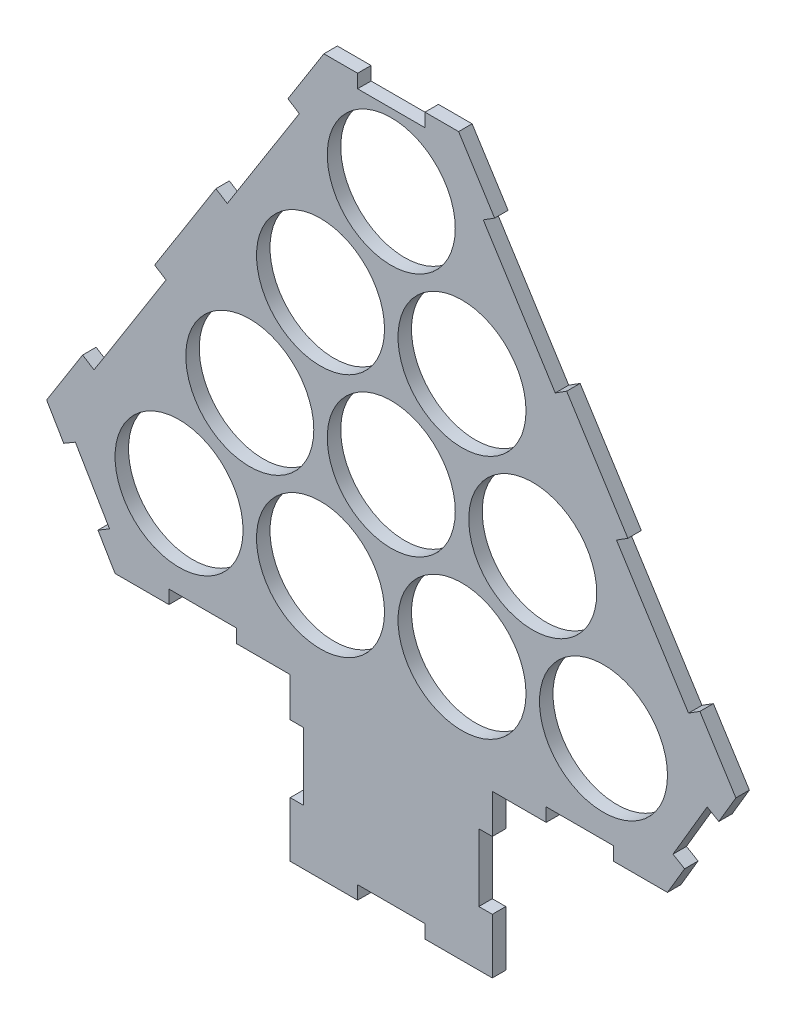
SolidWorks part; units mm, degrees
ref_plane "Plan de face" through (0, 0, 0) normal (0, 0, 1) x (1, 0, 0)
ref_plane "Plan de dessus" through (0, 0, 0) normal (0, 1, 0) x (1, 0, 0)
ref_plane "Plan de droite" through (0, 0, 0) normal (1, 0, 0) x (0, 0, -1)
sketch "Esquisse1" plane through (0, 0, 0) normal (0, 0, 1) x (1, 0, 0)
  line L0 (0, 0) -> (-371.1464, 0) construction
  line L1 (0, 0) -> (478.5179, 0) construction
  line L2 (0, 0) -> (0, 90.9327) construction
  line L3 (0, 90.9327) -> (-157.5, 90.9327) construction
  line L4 (0, 90.9327) -> (157.5, 90.9327) construction
  line L5 (0, 90.9327) -> (0, 181.8653) construction
  line L6 (0, 181.8653) -> (-52.5, 181.8653) construction
  line L7 (0, 181.8653) -> (52.5, 181.8653) construction
  line L8 (0, 181.8653) -> (0, 363.4062) construction
  line L12 (-255.7759, 10.9597) -> (-205, -75.1903)
  line L13 (205, -75.1903) -> (255.7759, 10.9597)
  line L14 (-50, 336.3537) -> (50, 336.3537)
  line L15 (-205, -75.1903) -> (205, -75.1903)
  line L16 (255.7759, 10.9597) -> (50, 336.3537)
  line L17 (-50, 336.3537) -> (-255.7759, 10.9597)
  line L18 (-50, 336.3537) -> (-50, -75.1903) construction
  line L19 (50, 336.3537) -> (50, -75.1903) construction
  circle A0 centre (-157.5, 0) radius 47.5
  circle A1 centre (-52.5, 0) radius 47.5
  circle A2 centre (52.5, 0) radius 47.5
  circle A3 centre (157.5, 0) radius 47.5
  circle A4 centre (-105, 90.9327) radius 47.5
  circle A5 centre (0, 90.9327) radius 47.5
  circle A6 centre (105, 90.9327) radius 47.5
  circle A7 centre (-52.5, 181.8653) radius 47.5
  circle A8 centre (52.5, 181.8653) radius 47.5
  circle A9 centre (0, 272.798) radius 47.5
  dimension "D1" = 95
  dimension "D2" = 95
  dimension "D3" = 95
  dimension "D4" = 95
  dimension "D5" = 105
  dimension "D6" = 52.5
  dimension "D7" = 52.5
  dimension "D8" = 105
  dimension "D9" = 95
  dimension "D10" = 95
  dimension "D11" = 95
  dimension "D12" = 105
  dimension "D13" = 105
  dimension "D14" = 105
  dimension "D15" = 95
  dimension "D16" = 95
  dimension "D17" = 105
  dimension "D18" = 52.5
  dimension "D19" = 52.5
  dimension "D20" = 95
  dimension "D21" = 105
  dimension "D27" = 205
  dimension "D22" = 385
  dimension "D23" = 385
  dimension "D24" = 410
  dimension "D25" = 32.309
  dimension "D26" = 32.309
  dimension "D28" = 100
  dimension "D30" = 100
  dimension "D31" = 100
extrude "Boss.-Extru.1" add sketch "Esquisse1" along normal blind 10
sketch "Esquisse9" plane through (0, 0, 10) normal (0, 0, 1) x (1, 0, 0)
  line L0 (-205, -75.1903) -> (205, -75.1903) construction
  line L1 (-75, -75.1903) -> (75, -75.1903)
  line L2 (-75, -75.1903) -> (-75, -195.1903)
  line L3 (-75, -195.1903) -> (75, -195.1903)
  line L4 (75, -75.1903) -> (75, -195.1903)
  dimension "D1" = 150
  dimension "D2" = 120
  dimension "D3" = 75
extrude "Boss.-Extru.2" add sketch "Esquisse9" against normal blind 10
sketch "Esquisse10" plane through (0, 0, 10) normal (0, 0, 1) x (1, 0, 0)
  line L0 (-75, -75.1903) -> (-75, -195.1903) construction
  line L1 (-75, -104.2447) -> (-65, -104.2447)
  line L2 (-75, -104.2447) -> (-75, -154.2447)
  line L3 (-75, -154.2447) -> (-65, -154.2447)
  line L4 (-65, -104.2447) -> (-65, -154.2447)
  line L5 (-75, -195.1903) -> (75, -195.1903) construction
  line L6 (-25, -195.1903) -> (25, -195.1903)
  line L7 (-25, -195.1903) -> (-25, -185.1903)
  line L8 (-25, -185.1903) -> (25, -185.1903)
  line L9 (25, -195.1903) -> (25, -185.1903)
  line L10 (-205, -75.1903) -> (-75, -75.1903) construction
  line L11 (-115, -75.1903) -> (-165, -75.1903)
  line L12 (-115, -75.1903) -> (-115, -65.1903)
  line L13 (-115, -65.1903) -> (-165, -65.1903)
  line L14 (-165, -75.1903) -> (-165, -65.1903)
  line L15 (-217.694, -53.6528) -> (-209.079, -48.5752)
  line L16 (-255.7759, 10.9597) -> (-205, -75.1903) construction
  line L17 (-209.079, -48.5752) -> (-234.4669, -5.5002)
  line L18 (-234.4669, -5.5002) -> (-243.0819, -10.5778)
  line L19 (-243.0819, -10.5778) -> (-217.694, -53.6528)
  line L20 (-229.0517, 53.2187) -> (-220.5999, 47.8738)
  line L21 (-50, 336.3537) -> (-255.7759, 10.9597) construction
  line L22 (-220.5999, 47.8738) -> (-167.1517, 132.3918)
  line L23 (-167.1517, 132.3918) -> (-175.6034, 137.7366)
  line L24 (-175.6034, 137.7366) -> (-229.0517, 53.2187)
  line L25 (-130.1724, 209.5768) -> (-121.7206, 204.232)
  line L26 (-121.7206, 204.232) -> (-68.2723, 288.7499)
  line L27 (-68.2723, 288.7499) -> (-76.7241, 294.0948)
  line L28 (-76.7241, 294.0948) -> (-130.1724, 209.5768)
  line L29 (50, 336.3537) -> (-50, 336.3537) construction
  line L30 (-25, 336.3537) -> (25, 336.3537)
  line L31 (-25, 336.3537) -> (-25, 326.3537)
  line L32 (-25, 326.3537) -> (25, 326.3537)
  line L33 (25, 336.3537) -> (25, 326.3537)
  line L34 (0, 336.3537) -> (0, -195.1903) construction
  line L35 (68.2723, 288.7499) -> (76.7241, 294.0948)
  line L36 (121.7206, 204.232) -> (68.2723, 288.7499)
  line L37 (130.1724, 209.5768) -> (121.7206, 204.232)
  line L38 (76.7241, 294.0948) -> (130.1724, 209.5768)
  line L39 (167.1517, 132.3918) -> (175.6034, 137.7366)
  line L40 (220.5999, 47.8738) -> (167.1517, 132.3918)
  line L41 (229.0517, 53.2187) -> (220.5999, 47.8738)
  line L42 (175.6034, 137.7366) -> (229.0517, 53.2187)
  line L43 (234.4669, -5.5002) -> (243.0819, -10.5778)
  line L44 (209.079, -48.5752) -> (234.4669, -5.5002)
  line L45 (217.694, -53.6528) -> (209.079, -48.5752)
  line L46 (243.0819, -10.5778) -> (217.694, -53.6528)
  line L47 (115, -65.1903) -> (165, -65.1903)
  line L48 (165, -75.1903) -> (165, -65.1903)
  line L49 (115, -75.1903) -> (165, -75.1903)
  line L50 (115, -75.1903) -> (115, -65.1903)
  line L51 (75, -154.2447) -> (65, -154.2447)
  line L52 (65, -104.2447) -> (65, -154.2447)
  line L53 (75, -104.2447) -> (65, -104.2447)
  line L54 (75, -104.2447) -> (75, -154.2447)
  dimension "D1" = 50
  dimension "D2" = 10
  dimension "D3" = 25
  dimension "D4" = 50
  dimension "D5" = 10
  dimension "D6" = 10
  dimension "D7" = 10
  dimension "D8" = 50
  dimension "D9" = 100
  dimension "D10" = 10
  dimension "D11" = 10
  dimension "D12" = 100
  dimension "D13" = 50
  dimension "D14" = 10
  dimension "D15" = 25
  dimension "D16" = 50
  dimension "D17" = 50
  dimension "D18" = 25
  dimension "D19" = 40
  dimension "D20" = 50
extrude "Enlèv. mat.-Extru.1" cut sketch "Esquisse10" against normal blind 10
